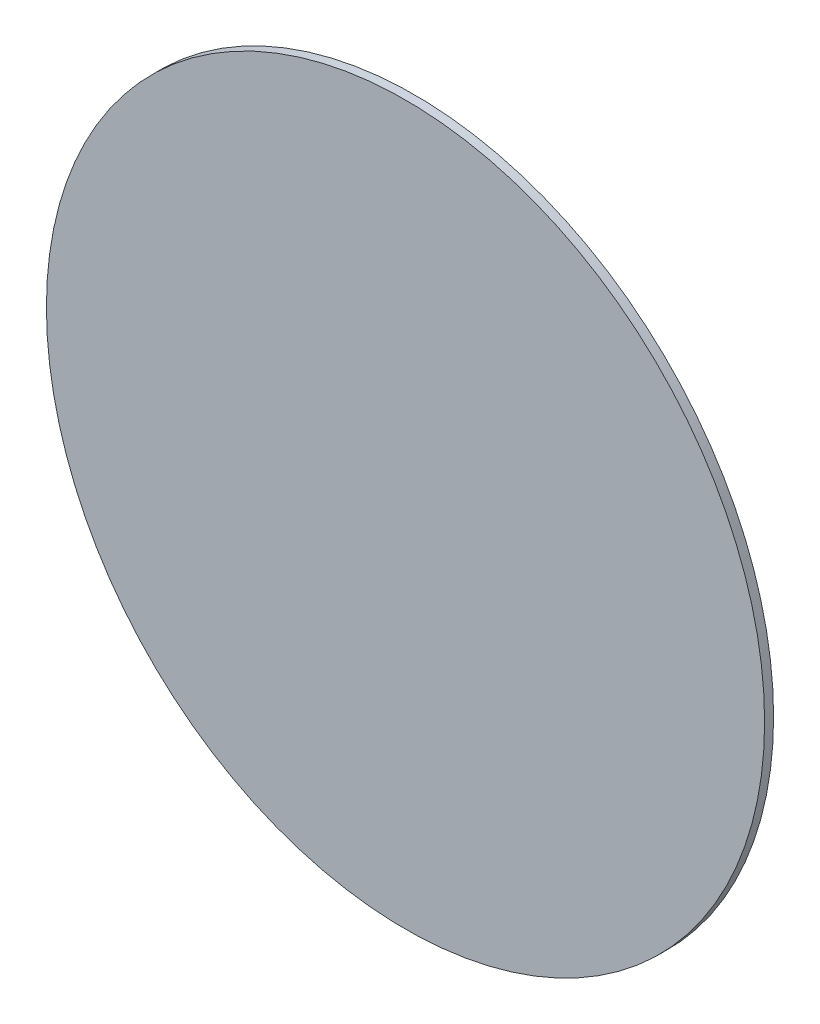
SolidWorks part; units mm, degrees
ref_plane "Alzado" through (0, 0, 0) normal (0, 0, 1) x (1, 0, 0)
ref_plane "Planta" through (0, 0, 0) normal (0, 1, 0) x (1, 0, 0)
ref_plane "Vista lateral" through (0, 0, 0) normal (1, 0, 0) x (0, 0, -1)
sketch "Croquis1" plane through (0, 0, 0) normal (0, 0, 1) x (1, 0, 0)
  circle A0 centre (0, 0) radius 20
  dimension "D1" = 40
extrude "Saliente-Extruir1" add sketch "Croquis1" along normal blind 0.5
